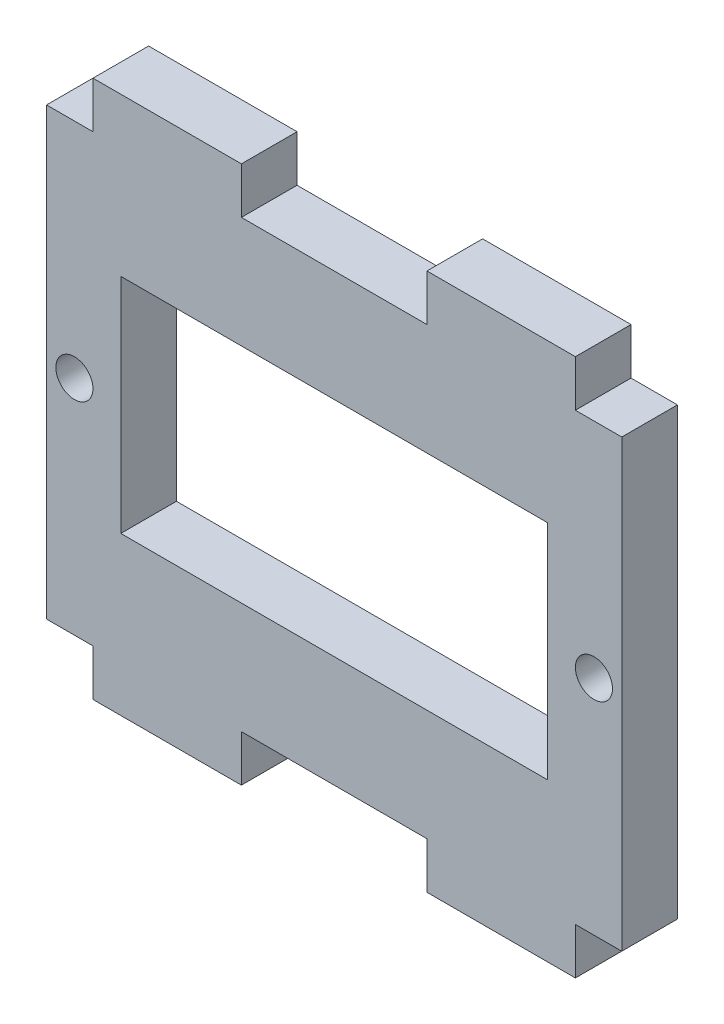
SolidWorks part; units mm, degrees
ref_plane "Front Plane" through (0, 0, 0) normal (0, 0, 1) x (1, 0, 0)
ref_plane "Top Plane" through (0, 0, 0) normal (0, 1, 0) x (1, 0, 0)
ref_plane "Right Plane" through (0, 0, 0) normal (1, 0, 0) x (0, 0, -1)
sketch "Sketch1" plane through (0, 0, 0) normal (0, 0, 1) x (1, 0, 0)
  line L0 (-17.5, 12) -> (17.5, 12)
  line L1 (-11.5, 6) -> (11.5, 6)
  line L2 (-11.5, 6) -> (-11.5, -6)
  line L3 (-11.5, -6) -> (11.5, -6)
  line L4 (11.5, 6) -> (11.5, -6)
  line L5 (-11.5, 6) -> (11.5, -6) construction
  line L6 (-11.5, -6) -> (11.5, 6) construction
  line L7 (17.5, 12) -> (17.5, -12)
  line L8 (-17.5, -12) -> (17.5, -12)
  line L9 (-17.5, 12) -> (-17.5, -12)
  line L10 (0, 6) -> (0, 0) construction
  line L11 (-13, 14.5) -> (-5, 14.5)
  line L12 (-13, 14.5) -> (-13, 12)
  line L13 (-13, 12) -> (-5, 12)
  line L14 (-5, 14.5) -> (-5, 12)
  line L15 (0, 0) -> (-11.5, 0) construction
  line L16 (5, 14.5) -> (5, 12)
  line L17 (13, 14.5) -> (13, 12)
  line L18 (13, 14.5) -> (5, 14.5)
  line L19 (13, -14.5) -> (5, -14.5)
  line L20 (13, -14.5) -> (13, -12)
  line L21 (5, -14.5) -> (5, -12)
  line L22 (-5, -14.5) -> (-5, -12)
  line L23 (-13, -14.5) -> (-13, -12)
  line L24 (-13, -14.5) -> (-5, -14.5)
  line L25 (17.5, -12) -> (15.5, -12)
  line L26 (-17.5, 12) -> (-15.5, 12)
  line L27 (-17.5, 12) -> (-17.5, -12)
  line L28 (-17.5, -12) -> (-15.5, -12)
  line L29 (-15.5, 12) -> (-15.5, -12)
  line L30 (15.5, 12) -> (15.5, -12)
  line L31 (17.5, 12) -> (15.5, 12)
  line L32 (17.5, 12) -> (17.5, -12)
  circle A0 centre (-14, 0) radius 1
  circle A1 centre (14, 0) radius 1
  point P0 (0, 0)
  dimension "D7" = 2
  dimension "D1" = 12
  dimension "D2" = 23
  dimension "D4" = 4.5
  dimension "D5" = 2.5
  dimension "D6" = 8
  dimension "D8" = 2.5
  dimension "D9" = 2.5
  dimension "D3" = 6
extrude "Boss-Extrude1" add sketch "Sketch1" along normal mid plane 3 contours L0 L9 L8 L7 L1 L4 L3 L2 A0 A1 | L14 L11 L12 L0 | L17 L18 L16 L0 | L23 L24 L22 L8 | L21 L19 L20 L8
